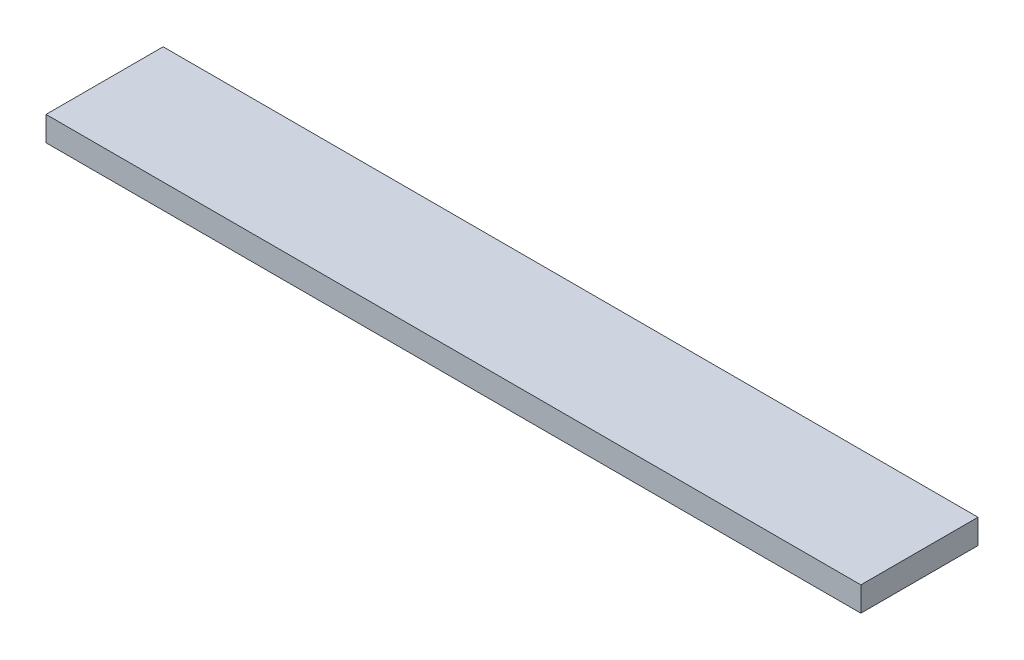
SolidWorks part; units mm, degrees
material "Oak"
ref_plane "Front Plane" through (0, 0, 0) normal (0, 0, 1) x (1, 0, 0)
ref_plane "Top Plane" through (0, 0, 0) normal (0, 1, 0) x (1, 0, 0)
ref_plane "Right Plane" through (0, 0, 0) normal (1, 0, 0) x (0, 0, -1)
sketch "Sketch1" plane through (0, 0, 0) normal (0, 1, 0) x (1, 0, 0)
  line L1 (0, 0) -> (631.7488, 0)
  line L2 (0, 0) -> (0, 90.8304)
  line L3 (0, 90.8304) -> (631.7488, 90.8304)
  line L4 (631.7488, 0) -> (631.7488, 90.8304)
  dimension "D1" = 90.8304
  dimension "D2" = 631.7488
extrude "Boss-Extrude1" add sketch "Sketch1" along normal blind 19.05
